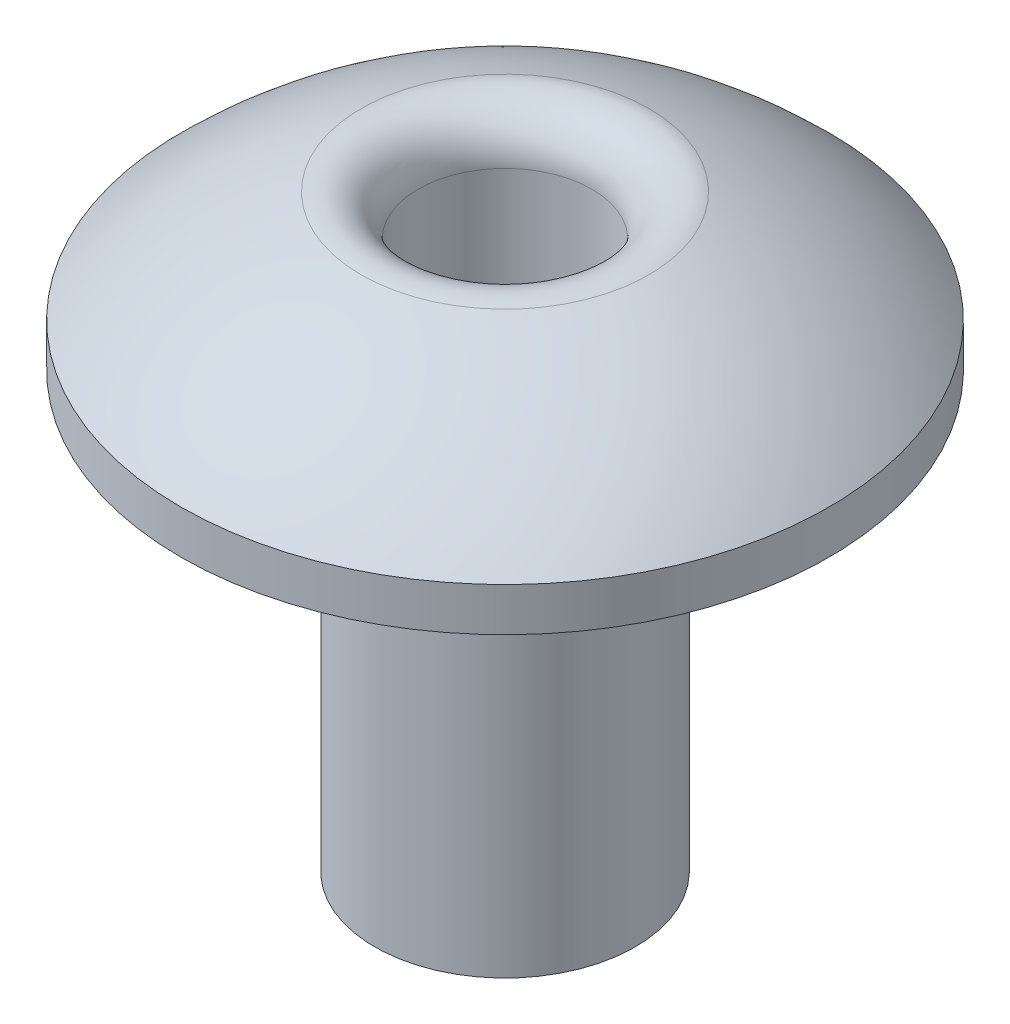
SolidWorks part; units mm, degrees
ref_plane "Front Plane" through (0, 0, 0) normal (0, 0, 1) x (1, 0, 0)
ref_plane "Top Plane" through (0, 0, 0) normal (0, 1, 0) x (1, 0, 0)
ref_plane "Right Plane" through (0, 0, 0) normal (1, 0, 0) x (0, 0, -1)
sketch "Sketch2" plane through (0, 0, 0) normal (1, 0, 0) x (0, 0, -1)
  line L0 (0, 0) -> (-62178.7483, 0) construction
  line L1 (0, 0) -> (0, 62178.7483) construction
  line L3 (0, 1.5453) -> (0, 0)
  line L5 (-3.7307, 0) -> (-3.7307, -0.5)
  line L6 (-3.7307, -0.5) -> (0, -0.5)
  line L7 (0, -0.5) -> (0, 0)
  arc A0 (-3.7307, 0) -> (0, 1.5453) centre (0, -3.7307) cw
  point P8 (0, 0)
  dimension "D1" = 0.5
revolve "Revolve2" add sketch "Sketch2" angle 360 about L7
sketch "Sketch3" plane through (0, -0.5, 0) normal (0, -1, 0) x (1, 0, 0)
  circle A0 centre (0, 0) radius 1.5
  dimension "D1" = 3
extrude "Boss-Extrude1" add sketch "Sketch3" along normal blind 5
sketch "Sketch4" plane through (0, -5.5, 0) normal (0, -1, 0) x (1, 0, 0)
  circle A0 centre (0, 0) radius 1
extrude "Cut-Extrude1" cut sketch "Sketch4" against normal through all
fillet "Fillet1" radius 0.5 1 edges at (0, 1.4497, -1)
